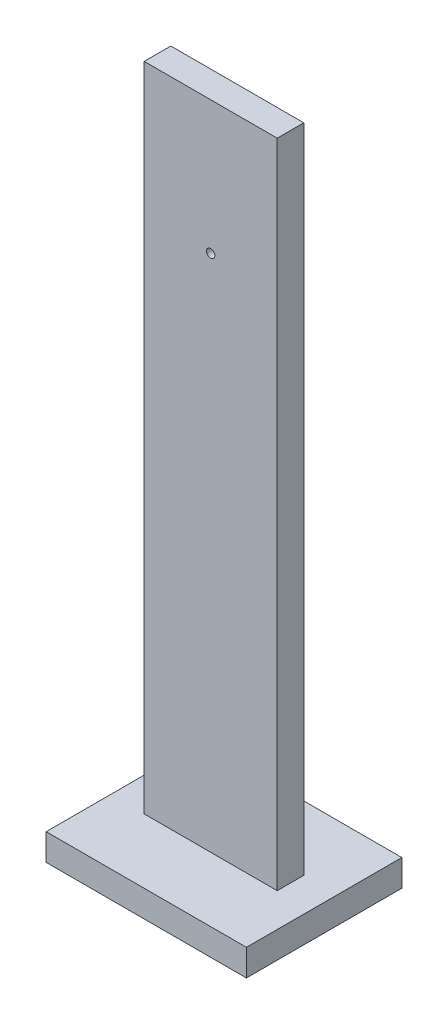
SolidWorks part; units mm, degrees
ref_plane "Alzado" through (0, 0, 0) normal (0, 0, 1) x (1, 0, 0)
ref_plane "Planta" through (0, 0, 0) normal (0, 1, 0) x (1, 0, 0)
ref_plane "Vista lateral" through (0, 0, 0) normal (1, 0, 0) x (0, 0, -1)
sketch "Croquis1" plane through (0, 0, 0) normal (0, 0, 1) x (1, 0, 0)
  line L0 (0, 150) -> (0, 250) construction
  line L1 (-50, -250) -> (50, -250)
  line L2 (-50, -250) -> (-50, 250)
  line L3 (-50, 250) -> (50, 250)
  line L4 (50, -250) -> (50, 250)
  line L5 (-50, -250) -> (50, 250) construction
  line L6 (-50, 250) -> (50, -250) construction
  circle A0 centre (0, 150) radius 3.125
  point P0 (0, 0)
  dimension "D3" = 6.25
  dimension "D1" = 500
  dimension "D2" = 100
  dimension "D4" = 100
extrude "Saliente-Extruir1" add sketch "Croquis1" along normal mid plane 20
sketch "Croquis2" plane through (0, -250, 0) normal (0, -1, 0) x (1, 0, 0)
  line L1 (-75.2798, -58.4348) -> (75.2798, -58.4348)
  line L2 (-75.2798, -58.4348) -> (-75.2798, 58.4348)
  line L3 (-75.2798, 58.4348) -> (75.2798, 58.4348)
  line L4 (75.2798, -58.4348) -> (75.2798, 58.4348)
  line L5 (-75.2798, -58.4348) -> (75.2798, 58.4348) construction
  line L6 (-75.2798, 58.4348) -> (75.2798, -58.4348) construction
  point P0 (0, 0)
extrude "Saliente-Extruir2" add sketch "Croquis2" along normal mid plane 20
